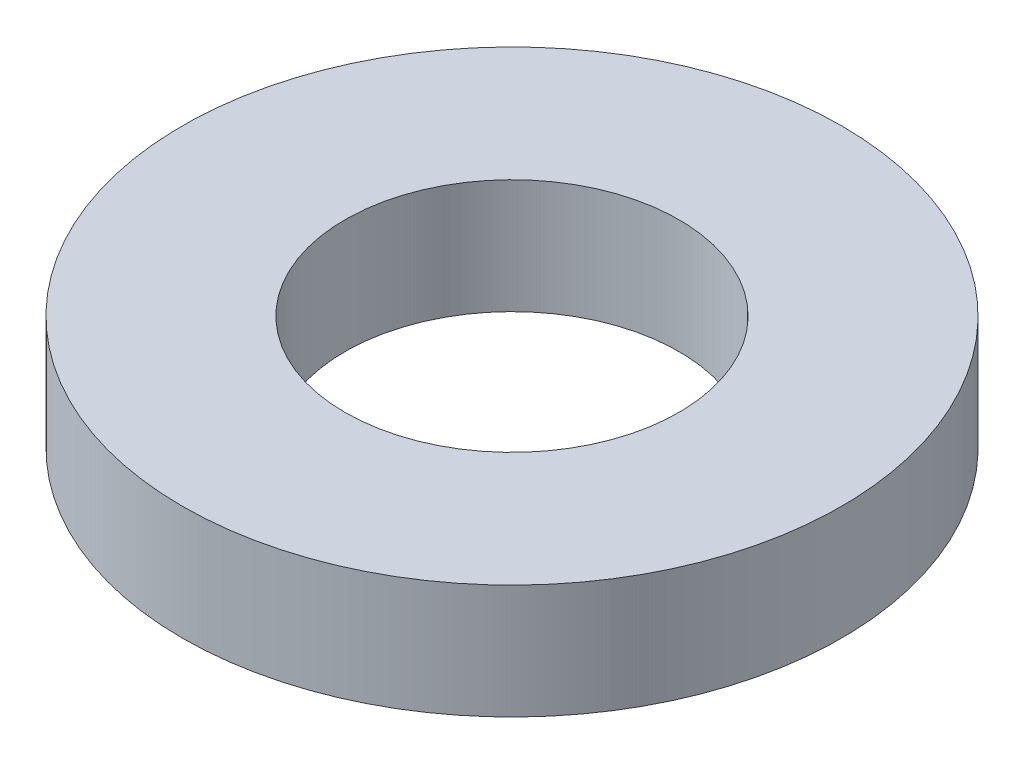
SolidWorks part; units mm, degrees
ref_plane "Front Plane" through (0, 0, 0) normal (0, 0, 1) x (1, 0, 0)
ref_plane "Top Plane" through (0, 0, 0) normal (0, 1, 0) x (1, 0, 0)
ref_plane "Right Plane" through (0, 0, 0) normal (1, 0, 0) x (0, 0, -1)
sketch "Sketch1" plane through (0, 0, 0) normal (0, 1, 0) x (1, 0, 0)
  circle A0 centre (0, 0) radius 2.413
  circle A1 centre (0, 0) radius 4.7625
  dimension "D1" = 4.826
  dimension "D2" = 9.525
extrude "Boss-Extrude1" add sketch "Sketch1" along normal blind 1.651
